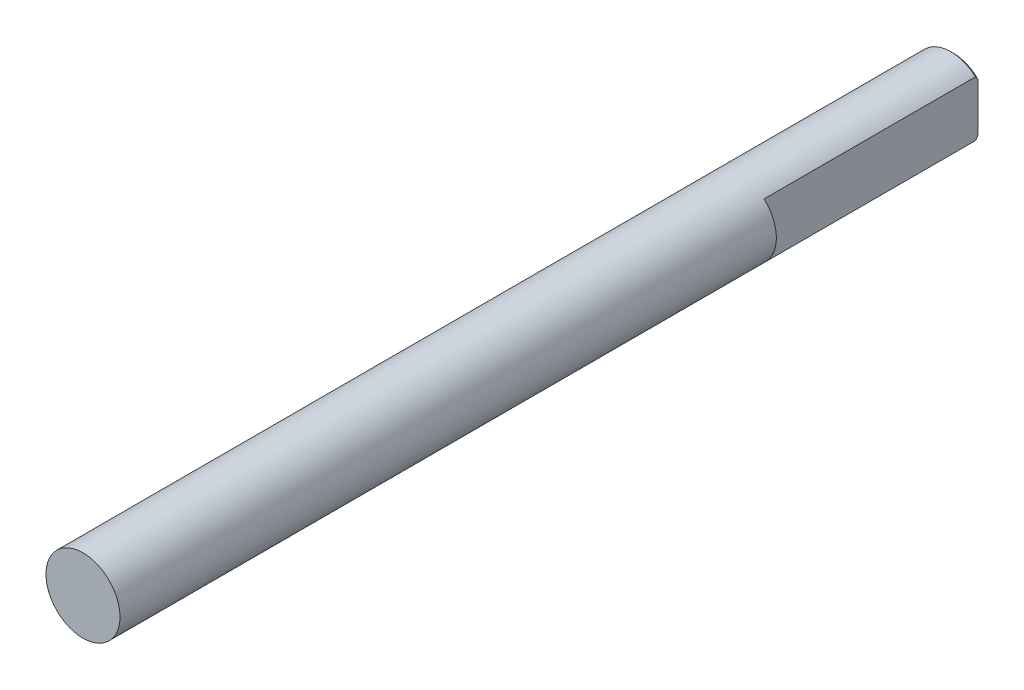
SolidWorks part; units mm, degrees
ref_plane "Спереди" through (0, 0, 0) normal (0, 0, 1) x (1, 0, 0)
ref_plane "Сверху" through (0, 0, 0) normal (0, 1, 0) x (1, 0, 0)
ref_plane "Справа" through (0, 0, 0) normal (1, 0, 0) x (0, 0, -1)
sketch "Эскиз1" plane through (0, 0, 0) normal (0, 0, 1) x (1, 0, 0)
  circle A0 centre (0, 0) radius 1.5
  dimension "D1" = 3
extrude "Бобышка-Вытянуть1" add sketch "Эскиз1" along normal blind 26.6
sketch "Эскиз2" plane through (0, 0, 0) normal (0, 0, -1) x (-1, 0, 0)
  circle A0 centre (0, 0) radius 1.5
  dimension "D1" = 3
extrude "Бобышка-Вытянуть2" add sketch "Эскиз2" along normal blind 8.67
chamfer "Фаска1" distance 0.1 angle 45 1 edges at (-1.5, 0, -8.67)
sketch "Эскиз3" plane through (0, 0, -8.67) normal (0, 0, -1) x (-1, 0, 0)
  line L1 (-1, 1.5) -> (1.5, 1.5)
  line L2 (-1, 1.5) -> (-1, -1.5)
  line L3 (-1, -1.5) -> (1.5, -1.5)
  line L4 (1.5, 1.5) -> (1.5, -1.5)
  dimension "D1" = 3
  dimension "D2" = 2.5
  dimension "D3" = 1
  dimension "D4" = 1.5
extrude "Вырез-Вытянуть1" cut sketch "Эскиз3" against normal blind 8.67 flip side to cut
